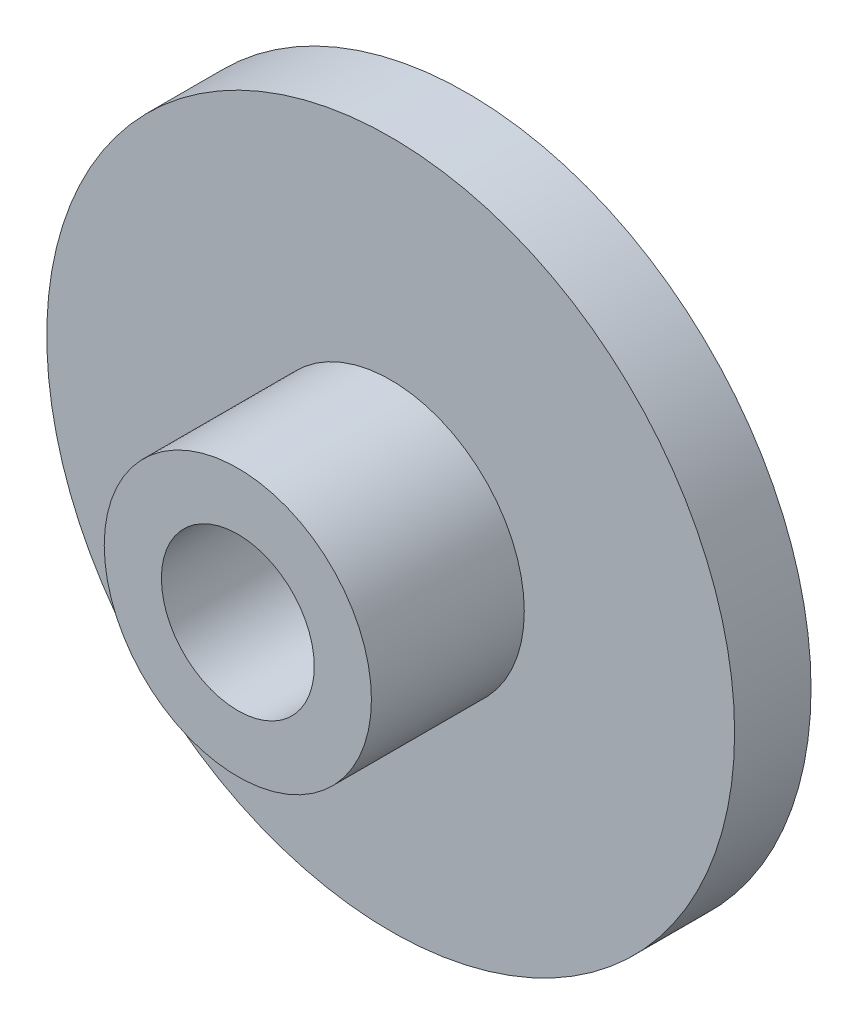
SolidWorks part; units mm, degrees
ref_plane "Front Plane" through (0, 0, 0) normal (0, 0, 1) x (1, 0, 0)
ref_plane "Top Plane" through (0, 0, 0) normal (0, 1, 0) x (1, 0, 0)
ref_plane "Right Plane" through (0, 0, 0) normal (1, 0, 0) x (0, 0, -1)
sketch "Sketch1" plane through (0, 0, 0) normal (0, 0, 1) x (1, 0, 0)
  circle A0 centre (0, 0) radius 14.2875
extrude "Boss-Extrude1" add sketch "Sketch1" along normal blind 3.175
sketch "Sketch2" plane through (0, 0, 3.175) normal (0, 0, 1) x (1, 0, 0)
  circle A0 centre (0, 0) radius 5.5499
extrude "Boss-Extrude2" add sketch "Sketch2" along normal blind 6.35
sketch "Sketch3" plane through (0, 0, 0) normal (0, 0, -1) x (-1, 0, 0)
  circle A0 centre (0, 0) radius 3.175
extrude "Cut-Extrude1" cut sketch "Sketch3" against normal blind 11.43
